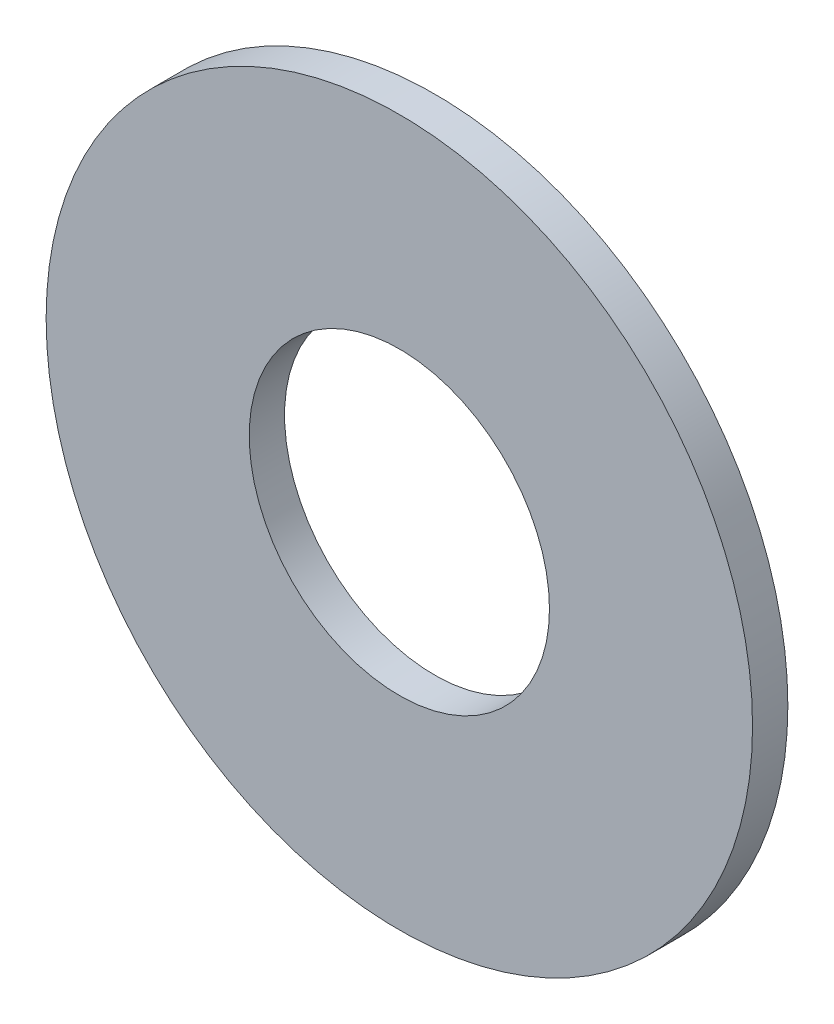
SolidWorks part; units mm, degrees
ref_plane "Спереди" through (0, 0, 0) normal (0, 0, 1) x (1, 0, 0)
ref_plane "Сверху" through (0, 0, 0) normal (0, 1, 0) x (1, 0, 0)
ref_plane "Справа" through (0, 0, 0) normal (1, 0, 0) x (0, 0, -1)
sketch "Эскиз1" plane through (0, 0, 0) normal (0, 0, 1) x (1, 0, 0)
  circle A0 centre (0, 0) radius 4.25
  circle A1 centre (0, 0) radius 10
  dimension "D1" = 8.5
  dimension "D2" = 20
extrude "Бобышка-Вытянуть1" add sketch "Эскиз1" along normal blind 1 contours A1 | A0
equation "\"d1\"= 8'внутренний диаметр"
equation "\"d2\"= 20'внешний диаметр"
equation "\"D2@Эскиз1\"=\"d2\""
equation "\"D1@Эскиз1\"=\"d1\"+0.5"
equation "\"h\"= 1'толщина"
equation "\"D1@Бобышка-Вытянуть1\"=\"h\""
